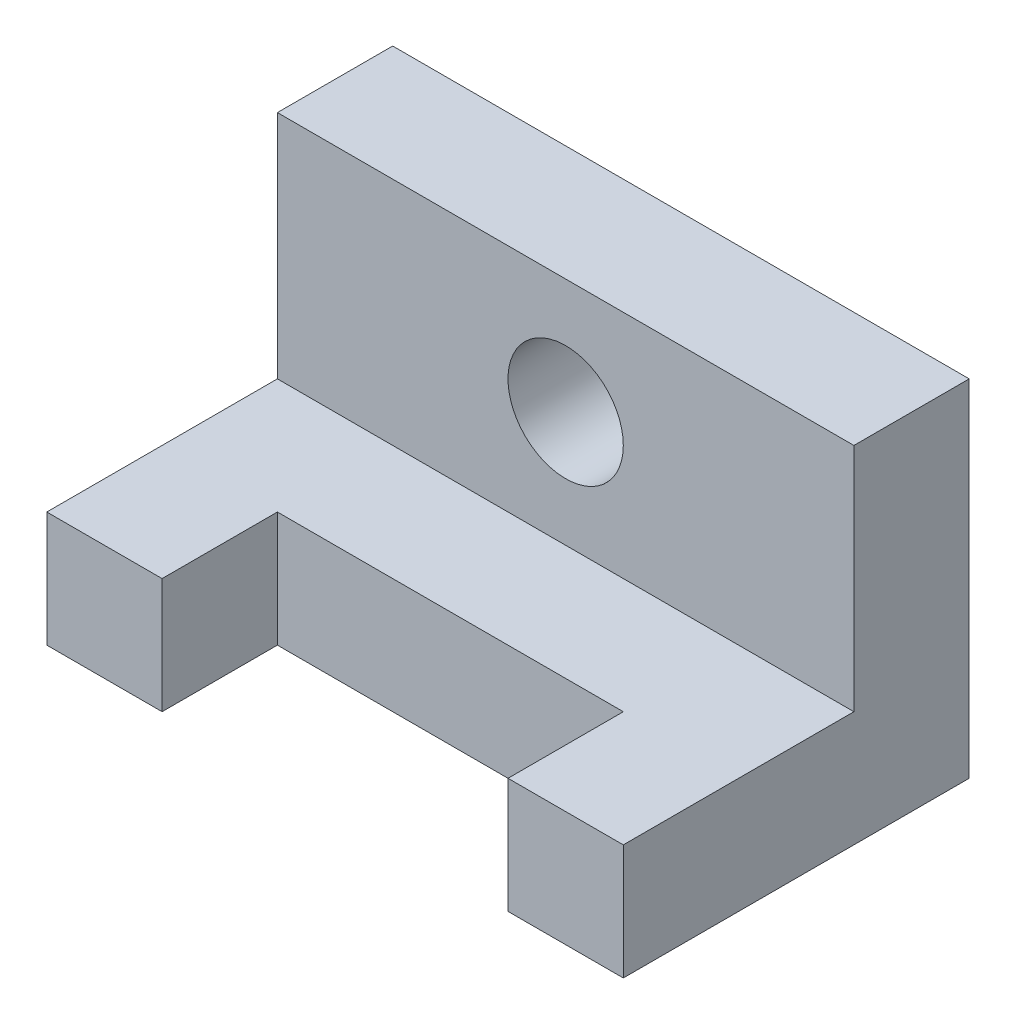
SolidWorks part; units mm, degrees
ref_plane "Front Plane" through (0, 0, 0) normal (0, 0, 1) x (1, 0, 0)
ref_plane "Top Plane" through (0, 0, 0) normal (0, 1, 0) x (1, 0, 0)
ref_plane "Right Plane" through (0, 0, 0) normal (1, 0, 0) x (0, 0, -1)
sketch "Sketch1" plane through (0, 0, 0) normal (1, 0, 0) x (0, 0, -1)
  line L0 (0, 60) -> (0, 0)
  line L1 (0, 55) -> (0, -55) construction
  line L2 (0, 0) -> (-60, 0)
  line L3 (55, 0) -> (-55, 0) construction
  line L4 (-20, 60) -> (-20, 20)
  line L5 (-20, 20) -> (-60, 20)
  line L6 (0, 60) -> (-20, 60)
  line L7 (-60, 0) -> (-60, 20)
  dimension "D2" = 60
  dimension "D3" = 60
  dimension "D1" = 20
extrude "Boss-Extrude1" add sketch "Sketch1" along normal mid plane 100
sketch "Sketch2" plane through (0, 20, 0) normal (0, 1, 0) x (1, 0, 0)
  line L0 (50, -60) -> (-50, -60) construction
  line L1 (-30, -60) -> (30, -60)
  line L2 (-30, -60) -> (-30, -40)
  line L3 (-30, -40) -> (30, -40)
  line L4 (30, -60) -> (30, -40)
  line L5 (0, -33) -> (0, 33) construction
  point P6 (0, -40)
  dimension "D1" = 60
  dimension "D2" = 20
extrude "Cut-Extrude1" cut sketch "Sketch2" against normal up to next
sketch "Sketch3" plane through (0, 0, 20) normal (0, 0, 1) x (1, 0, 0)
  line L2 (0, 60) -> (0, 87.702) construction
  line L3 (-50, 40) -> (50, 40) construction
  line L4 (-50, 60) -> (-50, 20) construction
  line L5 (50, 60) -> (50, 20) construction
  circle A0 centre (0, 40) radius 10
  dimension "D1" = 20
extrude "Cut-Extrude2" cut sketch "Sketch3" against normal up to next
